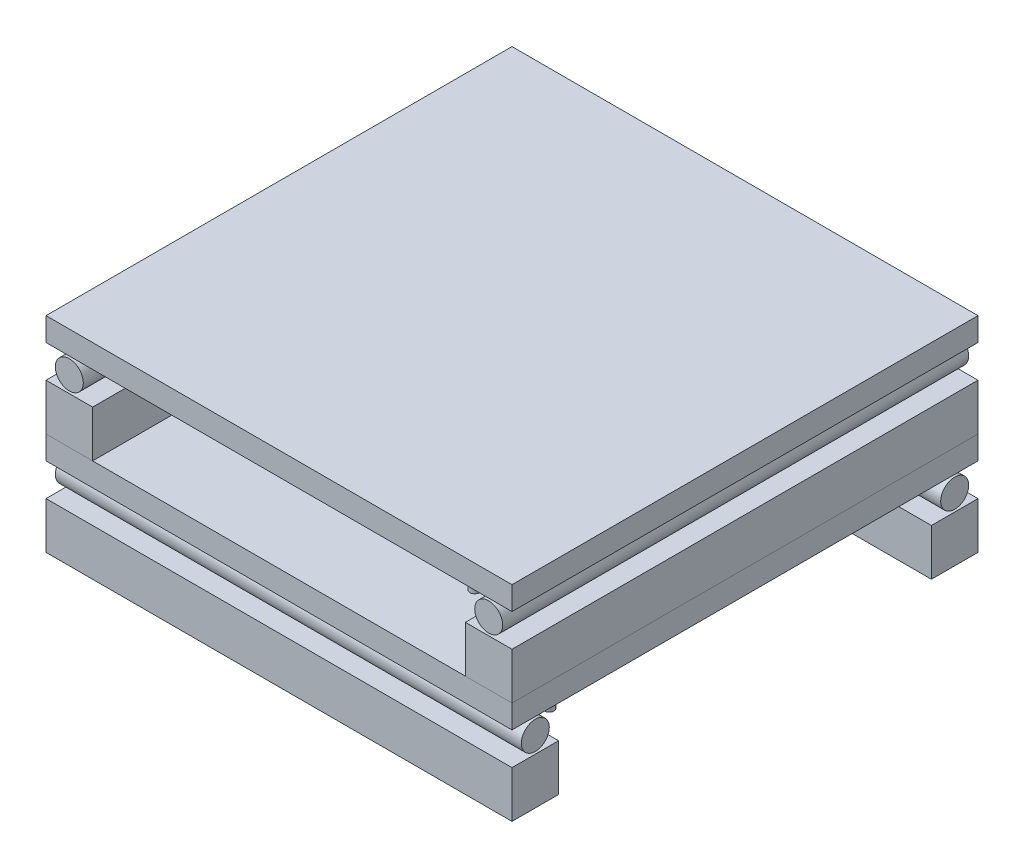
SolidWorks part; units mm, degrees
ref_plane "Front Plane" through (0, 0, 0) normal (0, 0, 1) x (1, 0, 0)
ref_plane "Top Plane" through (0, 0, 0) normal (0, 1, 0) x (1, 0, 0)
ref_plane "Right Plane" through (0, 0, 0) normal (1, 0, 0) x (0, 0, -1)
sketch "Sketch1" plane through (0, 0, 0) normal (0, 1, 0) x (1, 0, 0)
  line L1 (-50, 50) -> (50, 50)
  line L2 (-50, 50) -> (-50, 40)
  line L3 (-50, 40) -> (50, 40)
  line L4 (50, 50) -> (50, 40)
  line L5 (-50, 50) -> (50, 40) construction
  line L6 (-50, 40) -> (50, 50) construction
  line L7 (-50, -40) -> (50, -40)
  line L8 (-50, -40) -> (-50, -50)
  line L9 (-50, -50) -> (50, -50)
  line L10 (50, -40) -> (50, -50)
  line L11 (-50, -40) -> (50, -50) construction
  line L12 (-50, -50) -> (50, -40) construction
  point P0 (0, 45)
  point P6 (0, -45)
  dimension "D1" = 100
  dimension "D2" = 100
  dimension "D3" = 10
  dimension "D4" = 10
  dimension "D5" = 0
  dimension "D6" = 80
  dimension "D7" = 40
  dimension "D8" = 0
extrude "Boss-Extrude1" add sketch "Sketch1" along normal blind 10
sketch "Sketch2" plane through (50, 0, 0) normal (1, 0, 0) x (0, 0, -1)
  line L0 (-50, 10) -> (-40, 10) construction
  line L1 (40, 10) -> (50, 10) construction
  line L2 (50, 10) -> (50, 0) construction
  line L3 (-50, 17) -> (50, 17)
  line L4 (-50, 17) -> (-50, 22)
  line L5 (-50, 22) -> (50, 22)
  line L6 (50, 17) -> (50, 22)
  line L7 (-50, 10) -> (-50, 0) construction
  circle A0 centre (-45, 13.5) radius 3
  circle A1 centre (45, 13.5) radius 3
  dimension "D1" = 6
  dimension "D2" = 6
  dimension "D8" = 5
  dimension "D10" = 5
  dimension "D3" = 3.5
  dimension "D4" = 3.5
  dimension "D5" = 5
  dimension "D6" = 3.5
  dimension "D7" = 0
  dimension "D9" = 0
extrude "Boss-Extrude2" add sketch "Sketch2" against normal blind 100 separate body
sketch "Sketch3" plane through (0, 17, 0) normal (0, -1, 0) x (1, 0, 0)
  line L0 (50, 40) -> (-50, 40) construction
  line L2 (50, 50) -> (50, -50) construction
  line L3 (-50, 50) -> (-50, -50) construction
  circle A0 centre (45, 37) radius 1
  circle A1 centre (-45, 37) radius 1
  dimension "D1" = 3
  dimension "D2" = 3
  dimension "D3" = 5
  dimension "D4" = 5
extrude "Boss-Extrude3" add sketch "Sketch3" along normal blind 5
sketch "Sketch6" plane through (0, 12, 0) normal (0, -1, 0) x (1, 0, 0)
  circle A0 centre (24.312, 37) radius 1
  circle A1 centre (45, 37) radius 1 construction
  dimension "D1" = 2
  dimension "D2" = 0
extrude "Boss-Extrude4" add sketch "Sketch6" along normal mid plane 5 separate body
sketch "Sketch7" plane through (0, 9.5, 0) normal (0, -1, 0) x (1, 0, 0)
  circle A0 centre (24.312, 37) radius 3
extrude "Boss-Extrude5" add sketch "Sketch7" along normal blind 5
ref_plane "Plane1" through (0, 0, 0) normal (-0.7071, 0, 0.7071) x (0.7071, 0, 0.7071)
pattern_linear "LPattern1" count 2 spacing 22 along (0, 1, 0) of bodies 102 108 103 106 101 104
mirror "Mirror2" about plane through (0, 0, 0) normal (-0.7071, 0, 0.7071) of bodies 118 117 116 114 115 126
delete or keep bodies "Body-Delete1" type delete bodies bodies 115
delete or keep bodies "Body-Delete2" type delete bodies bodies 118
delete or keep bodies "Body-Delete3" type delete bodies bodies 114
delete or keep bodies "Body-Delete4" type delete bodies bodies 116
delete or keep bodies "Body-Delete5" type delete bodies bodies 117
delete or keep bodies "Body-Delete6" type delete bodies bodies 126
